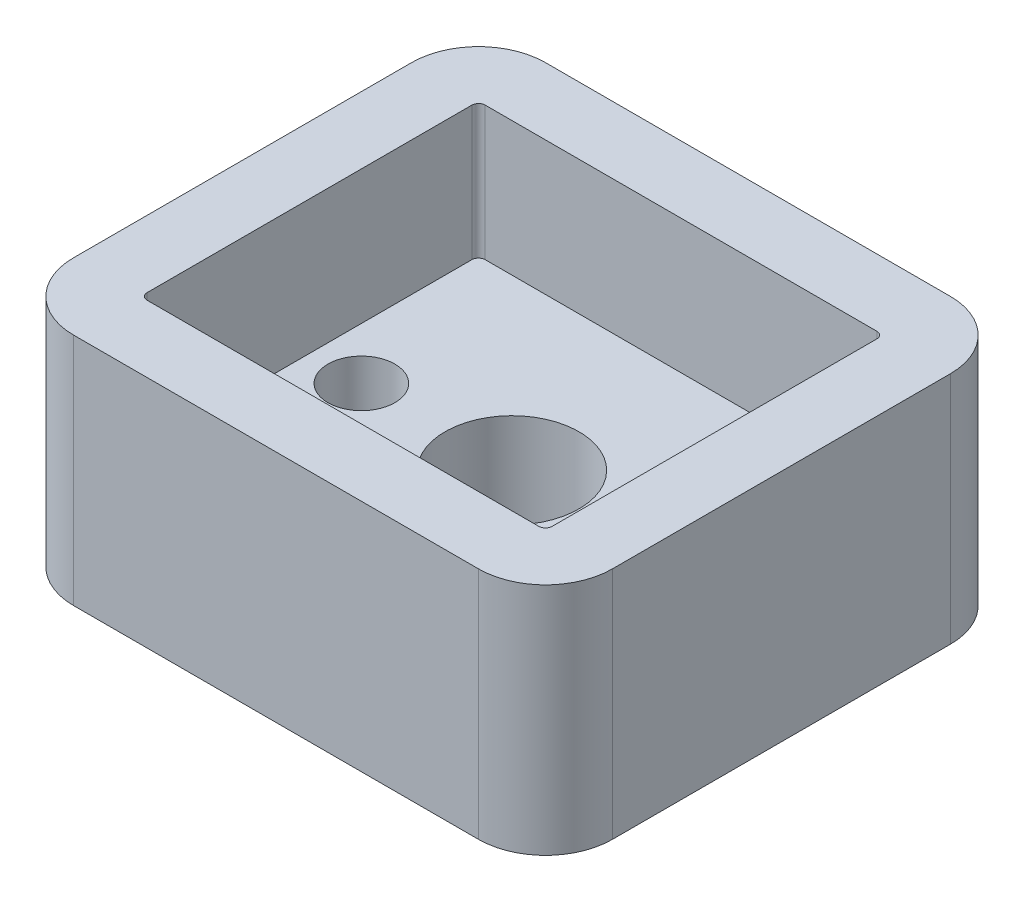
SolidWorks part; units mm, degrees
ref_plane "Front Plane" through (0, 0, 0) normal (0, 0, 1) x (1, 0, 0)
ref_plane "Top Plane" through (0, 0, 0) normal (0, 1, 0) x (1, 0, 0)
ref_plane "Right Plane" through (0, 0, 0) normal (1, 0, 0) x (0, 0, -1)
sketch "Sketch1" plane through (0, 0, 0) normal (0, 1, 0) x (1, 0, 0)
  line L0 (0, 5.05) -> (0, 7.05) construction
  line L1 (-8.05, 7.05) -> (8.05, 7.05)
  line L2 (-8.05, 7.05) -> (-8.05, -7.05)
  line L3 (-8.05, -7.05) -> (8.05, -7.05)
  line L4 (8.05, 7.05) -> (8.05, -7.05)
  line L5 (0, -5.05) -> (0, 0) construction
  line L6 (-8.05, 0) -> (-6.05, 0) construction
  line L11 (0, -5.05) -> (0, 0) construction
  line L12 (0, 0) -> (6.05, 0) construction
  line L13 (0, 0) -> (6.05, 0) construction
  point P4 (0, 0)
  point P233 (0, 0)
  point P296 (0, 0)
  dimension "D1" = 16.1
  dimension "D2" = 14.1
extrude "Boss-Extrude1" add sketch "Sketch1" along normal blind 7
sketch "Sketch3" plane through (0, 7, 0) normal (0, 1, 0) x (1, 0, 0)
  line L0 (-3.85, 0) -> (3.85, 0) construction
  line L1 (-6.05, 5.05) -> (6.05, 5.05)
  line L2 (-6.05, 5.05) -> (-6.05, -5.05)
  line L3 (-6.05, -5.05) -> (6.05, -5.05)
  line L4 (6.05, 5.05) -> (6.05, -5.05)
  line L5 (0, -5.05) -> (0, 5.05) construction
  line L6 (-6.05, 0) -> (6.05, 0) construction
  line L7 (0, -3.85) -> (0, 3.85) construction
  point P4 (0, 0)
  point P316 (0, 0)
  dimension "D1" = 10.1
  dimension "D2" = 12.1
extrude "Cut-Extrude1" cut sketch "Sketch3" against normal offset from surface (4 mm away) 3 up to plane "Top Plane"
hole_wizard "CSK for M1.6 Countersunk Flat Head Screw1" positions "Sketch6" profile "Sketch7" countersink size "M1.6" standard "ISO" end condition up to next
sketch "Sketch6" plane through (0, 0, 0) normal (0, -1, 0) x (-1, 0, 0)
  line L0 (-3.85, 0) -> (3.85, 0) construction
  line L1 (0, 3.85) -> (0, -3.85) construction
  point P0 (4.5, 0)
  point P3 (0, 0)
  point P8 (0, 0)
  point P9 (-4.5, 0)
  dimension "D1" = 4.5
sketch "Sketch7" plane through (-4.5, 0, 0) normal (1, 0, 0) x (0, 0, -1)
  line L0 (0, 0) -> (0, 3)
  line L1 (0, 3) -> (1, 3)
  line L2 (1, 3) -> (1, 1)
  line L3 (1, 1) -> (2, 0)
  line L5 (2, 0) -> (0, 0)
  line L6 (-1, 1) -> (-2, 0) construction
  line L11 (0, -6.35) -> (0, 107.95) construction
  dimension "Thru Hole Dia." = 2
  dimension "Thru Hole Depth" = 3
  dimension "Near C'Sink Dia." = 4
  dimension "Near C'Sink Angle" = 90
sketch "Sketch8" plane through (0, 3, 0) normal (0, 1, 0) x (1, 0, 0)
  circle A0 centre (0, 0) radius 2
  dimension "D1" = 4
extrude "Cut-Extrude2" cut sketch "Sketch8" against normal through all
fillet "Fillet1" radius 2 4 edges at (-8.05, 3.5, -7.05) (8.05, 3.5, 7.05) (-8.05, 3.5, 7.05) (8.05, 3.5, -7.05)
fillet "Fillet2" radius 0.2 4 edges at (-6.05, 5, -5.05) (6.05, 5, -5.05) (-6.05, 5, 5.05) (6.05, 5, 5.05)
